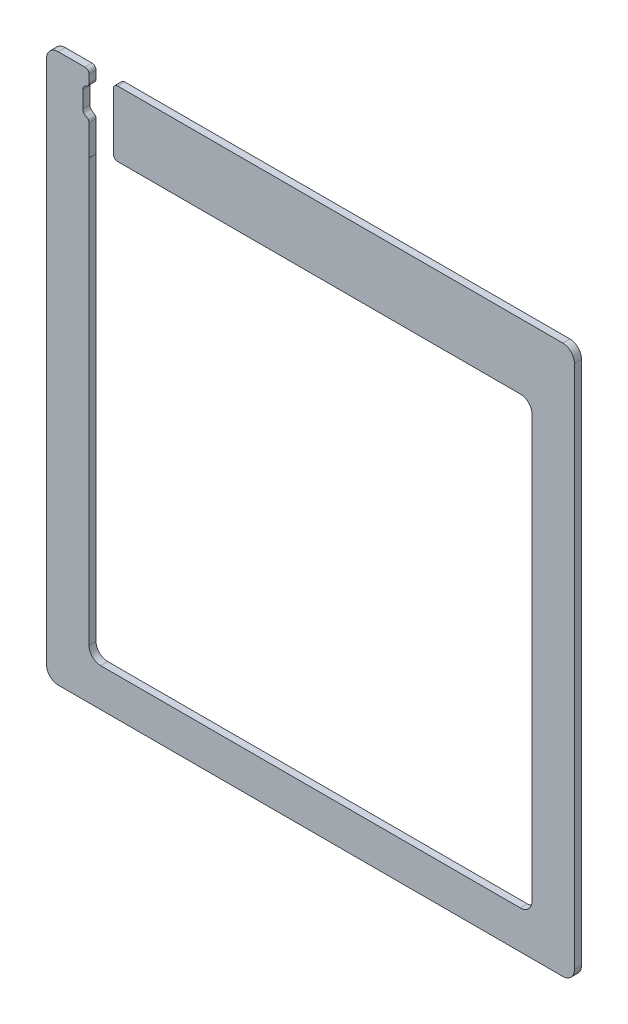
SolidWorks part; units mm, degrees
ref_plane "Front Plane" through (0, 0, 0) normal (0, 0, 1) x (1, 0, 0)
ref_plane "Top Plane" through (0, 0, 0) normal (0, 1, 0) x (1, 0, 0)
ref_plane "Right Plane" through (0, 0, 0) normal (1, 0, 0) x (0, 0, -1)
sketch "Sketch1" plane through (0, 0, 0) normal (0, 0, 1) x (1, 0, 0)
  line L1 (-161.925, -168.275) -> (161.925, -168.275)
  line L2 (-161.925, -168.275) -> (-161.925, 168.275)
  line L3 (-161.925, 168.275) -> (161.925, 168.275)
  line L4 (161.925, -168.275) -> (161.925, 168.275)
  line L5 (-161.925, -168.275) -> (161.925, 168.275) construction
  line L6 (-161.925, 168.275) -> (161.925, -168.275) construction
  point P0 (0, 0)
  dimension "D1" = 323.85
  dimension "D2" = 336.55
extrude "Boss-Extrude1" add sketch "Sketch1" along normal blind 4.3434
sketch "Sketch2" plane through (0, 0, 4.3434) normal (0, 0, 1) x (1, 0, 0)
  line L0 (-161.925, -168.275) -> (161.925, -168.275) construction
  line L1 (-135.89, -144.907) -> (135.89, -144.907)
  line L2 (-135.89, -144.907) -> (-135.89, 128.143)
  line L3 (-135.89, 128.143) -> (135.89, 128.143)
  line L4 (135.89, -144.907) -> (135.89, 128.143)
  line L5 (-135.89, -144.907) -> (135.89, 128.143) construction
  line L6 (-135.89, 128.143) -> (135.89, -144.907) construction
  line L7 (0, 168.275) -> (0, -168.275) construction
  line L8 (161.925, 168.275) -> (-161.925, 168.275) construction
  point P0 (0, -8.382)
  dimension "D1" = 271.78
  dimension "D2" = 273.05
  dimension "D3" = 23.368
extrude "Cut-Extrude1" cut sketch "Sketch2" against normal through all
fillet "Fillet1" radius 7.1437 8 edges at (135.89, -144.907, 2.1717) (135.89, 128.143, 2.1717) (-135.89, 128.143, 2.1717) (-135.89, -144.907, 2.1717) (-161.925, -168.275, 2.1717) (161.925, -168.275, 2.1717) (161.925, 168.275, 2.1717) (-161.925, 168.275, 2.1717)
sketch "Sketch3" plane through (0, 0, 4.3434) normal (0, 0, 1) x (1, 0, 0)
  line L0 (-136.525, 145.415) -> (-136.525, 155.575) construction
  line L1 (-139.7, 145.415) -> (-139.7, 155.575)
  line L2 (-133.35, 145.415) -> (-133.35, 155.575)
  line L3 (-161.925, 161.1312) -> (-161.925, -161.1313) construction
  line L5 (154.7812, 168.275) -> (-154.7812, 168.275) construction
  arc A0 (-139.7, 145.415) -> (-133.35, 145.415) centre (-136.525, 145.415) ccw
  arc A1 (-133.35, 155.575) -> (-139.7, 155.575) centre (-136.525, 155.575) ccw
  point P2 (-136.525, 150.495)
  dimension "D1" = 6.35
  dimension "D2" = 25.4
  dimension "D3" = 22.86
  dimension "D4" = 12.7
extrude "Cut-Extrude2" cut sketch "Sketch3" against normal through all
sketch "Sketch4" plane through (0, 0, 4.3434) normal (0, 0, 1) x (1, 0, 0)
  line L0 (-135.89, 168.275) -> (-120.9103, 168.275)
  line L1 (-135.89, 168.275) -> (-135.89, 121.3499)
  line L2 (-120.9103, 168.275) -> (-120.9103, 121.3499)
  line L3 (-135.89, 121.3499) -> (-120.9103, 121.3499)
  line L4 (154.7812, 168.275) -> (-154.7812, 168.275) construction
  line L5 (-135.89, 120.9992) -> (-135.89, -137.7633) construction
extrude "Cut-Extrude3" cut sketch "Sketch4" against normal through all
fillet "Fillet2" radius 2.54 5 edges at (-135.89, 168.275, 2.1717) (-120.9103, 168.275, 2.1717) (-120.9103, 128.143, 2.1717) (-135.89, 158.6859, 2.1717) (-135.89, 142.3041, 2.1717)
